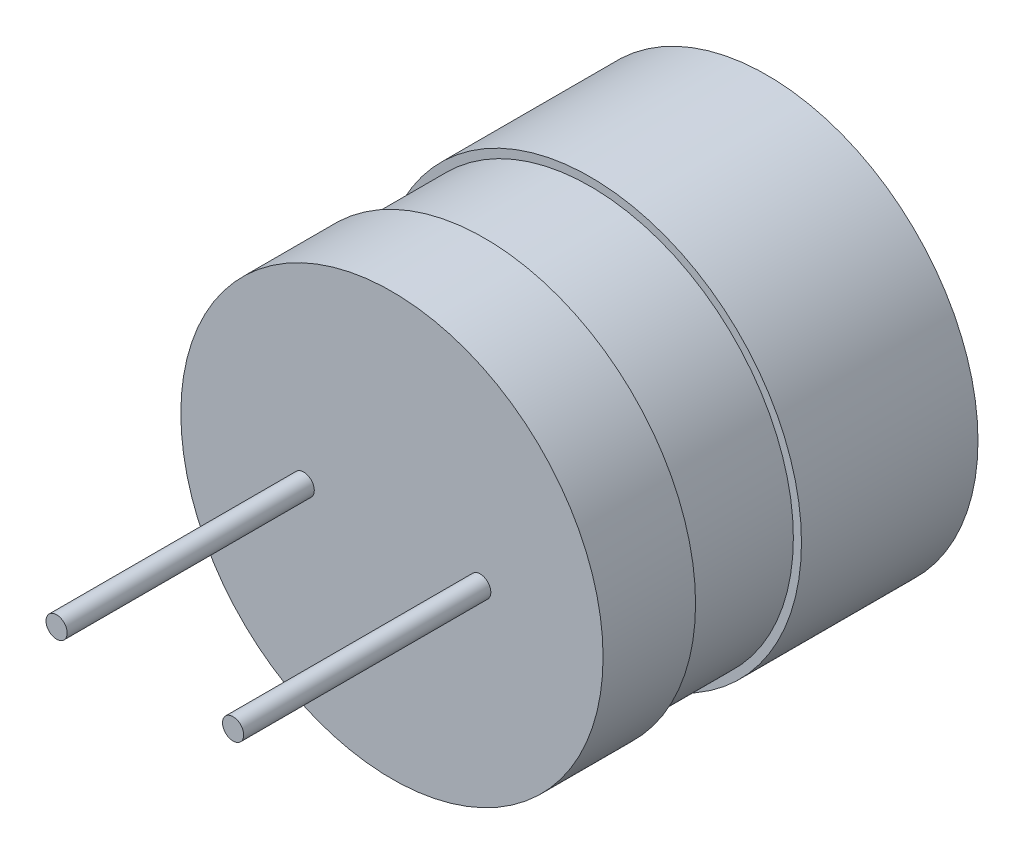
SolidWorks part; units mm, degrees
ref_plane "Ön Düzlem" through (0, 0, 0) normal (0, 0, 1) x (1, 0, 0)
ref_plane "Üst Düzlem" through (0, 0, 0) normal (0, 1, 0) x (1, 0, 0)
ref_plane "Sağ Düzlem" through (0, 0, 0) normal (1, 0, 0) x (0, 0, -1)
sketch "Sketch1" plane through (0, 0, 0) normal (0, 0, 1) x (1, 0, 0)
  circle A0 centre (0, 0) radius 5.98
  dimension "D1" = 11.96
extrude "Boss-Extrude1" add sketch "Sketch1" along normal blind 5
sketch "Sketch2" plane through (0, 0, 0) normal (0, 0, -1) x (-1, 0, 0)
  circle A0 centre (0, 0) radius 1.25
  dimension "D1" = 2.5
extrude "Cut-Extrude1" cut sketch "Sketch2" against normal blind 5
sketch "Sketch3" plane through (0, 0, 5) normal (0, 0, 1) x (1, 0, 0)
  circle A0 centre (0, 0) radius 5.75
  dimension "D1" = 11.5
extrude "Boss-Extrude2" add sketch "Sketch3" along normal blind 3
sketch "Sketch4" plane through (0, 0, 8) normal (0, 0, 1) x (1, 0, 0)
  circle A0 centre (0, 0) radius 5.98
extrude "Boss-Extrude3" add sketch "Sketch4" along normal blind 2.62
sketch "Sketch5" plane through (0, 0, 10.62) normal (0, 0, 1) x (1, 0, 0)
  circle A0 centre (-2.5, 0) radius 0.645
  circle A1 centre (2.5, 0) radius 0.645
  dimension "D1" = 1.29
  dimension "D3" = 2.5
  dimension "D4" = 1.29
  dimension "D2" = 2.5
extrude "Boss-Extrude4" add sketch "Sketch5" along normal blind 7
sketch "Sketch6" plane through (0, 0, 17.62) normal (0, 0, 1) x (1, 0, 0)
  circle A0 centre (-2.5, 0) radius 0.3
  circle A1 centre (-2.5, 0) radius 0.645
  circle A2 centre (2.5, 0) radius 0.645
  circle A3 centre (2.5, 0) radius 0.3
  dimension "D1" = 0.6
  dimension "D2" = 0.6
extrude "Cut-Extrude2" cut sketch "Sketch6" against normal blind 7
